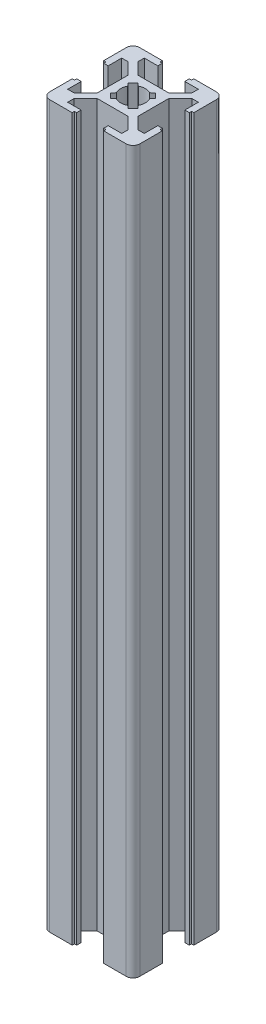
SolidWorks part; units mm, degrees
material "3.3547 (EN-AW 5083)"
ref_plane "Płaszczyzna przednia" through (0, 0, 0) normal (0, 0, 1) x (1, 0, 0)
ref_plane "Płaszczyzna górna" through (0, 0, 0) normal (0, 1, 0) x (1, 0, 0)
ref_plane "Płaszczyzna prawa" through (0, 0, 0) normal (1, 0, 0) x (0, 0, -1)
sketch "Szkic1" plane through (0, 0, 0) normal (0, 1, 0) x (1, 0, 0)
  line L0 (0, 10) -> (0, -10) construction
  line L1 (4.5, -4.5) -> (-4.5, -4.5)
  line L2 (4.5, -4.5) -> (4.5, 4.5)
  line L3 (4.5, 4.5) -> (-4.5, 4.5)
  line L4 (-4.5, -4.5) -> (-4.5, 4.5)
  line L5 (4.5, -4.5) -> (-4.5, 4.5) construction
  line L6 (4.5, 4.5) -> (-4.5, -4.5) construction
  line L7 (8.5, -10) -> (-8.5, -10)
  line L8 (10, -8.5) -> (10, 8.5)
  line L9 (8.5, 10) -> (-8.5, 10)
  line L10 (-10, -8.5) -> (-10, 8.5)
  line L11 (10, -10) -> (-10, 10) construction
  line L12 (10, 10) -> (-10, -10) construction
  line L13 (3.5, 10) -> (-3.5, 10)
  line L14 (-3.5, 10) -> (-3.5, 9.5)
  line L15 (-3.5, 9.5) -> (-3, 9.5)
  line L16 (-3, 9.5) -> (-3, 8.5)
  line L17 (-3, 8.5) -> (-6, 8.5)
  line L18 (-6, 8.5) -> (-6, 7.06)
  line L19 (-6, 7.06) -> (-3.4405, 4.5)
  line L20 (-1.9445, 3.0052) -> (-3.0052, 1.9445)
  line L21 (-1.9445, 3.0052) -> (-1.2713, 2.4385)
  line L22 (-3.0052, 1.9445) -> (-2.4385, 1.2713)
  line L23 (3.5, 10) -> (3.5, 9.5)
  line L24 (3.5, 9.5) -> (3, 9.5)
  line L25 (3, 9.5) -> (3, 8.5)
  line L26 (3, 8.5) -> (6, 8.5)
  line L27 (6, 8.5) -> (6, 7.06)
  line L28 (6, 7.06) -> (3.4405, 4.5)
  line L29 (1.9445, 3.0052) -> (3.0052, 1.9445)
  line L30 (1.9445, 3.0052) -> (1.2713, 2.4385)
  line L31 (3.0052, 1.9445) -> (2.4385, 1.2713)
  line L32 (1.9445, 3.0052) -> (1.2713, 2.4385)
  line L33 (3.0052, 1.9445) -> (1.9445, 3.0052)
  line L34 (3.0052, 1.9445) -> (2.4385, 1.2713)
  line L35 (7.06, 6) -> (4.5, 3.4405)
  line L36 (8.5, 6) -> (7.06, 6)
  line L37 (8.5, 3) -> (8.5, 6)
  line L38 (9.5, 3) -> (8.5, 3)
  line L39 (9.5, 3.5) -> (9.5, 3)
  line L40 (10, 3.5) -> (9.5, 3.5)
  line L41 (10, -3.5) -> (9.5, -3.5)
  line L42 (9.5, -3.5) -> (9.5, -3)
  line L43 (9.5, -3) -> (8.5, -3)
  line L44 (8.5, -3) -> (8.5, -6)
  line L45 (8.5, -6) -> (7.06, -6)
  line L46 (7.06, -6) -> (4.5, -3.4405)
  line L47 (3.0052, -1.9445) -> (2.4385, -1.2713)
  line L48 (3.0052, -1.9445) -> (1.9445, -3.0052)
  line L49 (1.9445, -3.0052) -> (1.2713, -2.4385)
  line L50 (3.0052, -1.9445) -> (2.4385, -1.2713)
  line L51 (1.9445, -3.0052) -> (3.0052, -1.9445)
  line L52 (1.9445, -3.0052) -> (1.2713, -2.4385)
  line L53 (6, -7.06) -> (3.4405, -4.5)
  line L54 (6, -8.5) -> (6, -7.06)
  line L55 (3, -8.5) -> (6, -8.5)
  line L56 (3, -9.5) -> (3, -8.5)
  line L57 (3.5, -9.5) -> (3, -9.5)
  line L58 (3.5, -10) -> (3.5, -9.5)
  line L59 (-3.5, -10) -> (-3.5, -9.5)
  line L60 (-3.5, -9.5) -> (-3, -9.5)
  line L61 (-3, -9.5) -> (-3, -8.5)
  line L62 (-3, -8.5) -> (-6, -8.5)
  line L63 (-6, -8.5) -> (-6, -7.06)
  line L64 (-6, -7.06) -> (-3.4405, -4.5)
  line L65 (-1.9445, -3.0052) -> (-1.2713, -2.4385)
  line L66 (-1.9445, -3.0052) -> (-3.0052, -1.9445)
  line L67 (-3.0052, -1.9445) -> (-2.4385, -1.2713)
  line L68 (-1.9445, -3.0052) -> (-1.2713, -2.4385)
  line L69 (-3.0052, -1.9445) -> (-1.9445, -3.0052)
  line L70 (-3.0052, -1.9445) -> (-2.4385, -1.2713)
  line L71 (-7.06, -6) -> (-4.5, -3.4405)
  line L72 (-8.5, -6) -> (-7.06, -6)
  line L73 (-8.5, -3) -> (-8.5, -6)
  line L74 (-9.5, -3) -> (-8.5, -3)
  line L75 (-9.5, -3.5) -> (-9.5, -3)
  line L76 (-10, -3.5) -> (-9.5, -3.5)
  line L77 (-10, 3.5) -> (-9.5, 3.5)
  line L78 (-9.5, 3.5) -> (-9.5, 3)
  line L79 (-9.5, 3) -> (-8.5, 3)
  line L80 (-8.5, 3) -> (-8.5, 6)
  line L81 (-8.5, 6) -> (-7.06, 6)
  line L82 (-7.06, 6) -> (-4.5, 3.4405)
  line L83 (-3.0052, 1.9445) -> (-2.4385, 1.2713)
  line L84 (-3.0052, 1.9445) -> (-1.9445, 3.0052)
  line L85 (-1.9445, 3.0052) -> (-1.2713, 2.4385)
  circle A0 centre (0, 0) radius 2.75
  arc A1 (10, -8.5) -> (8.5, -10) centre (8.5, -8.5) cw
  arc A2 (-10, -8.5) -> (-8.5, -10) centre (-8.5, -8.5) ccw
  arc A3 (10, 8.5) -> (8.5, 10) centre (8.5, 8.5) ccw
  arc A4 (-8.5, 10) -> (-10, 8.5) centre (-8.5, 8.5) ccw
  point P16 (0, 10)
  point P37 (-2.4749, 2.4749)
  dimension "D1" = 5.5
  dimension "D12" = 1.5
  dimension "D2" = 9
  dimension "D3" = 20
  dimension "D4" = 20
  dimension "D5" = 7
  dimension "D6" = 0.5
  dimension "D7" = 0.5
  dimension "D8" = 1
  dimension "D9" = 3
  dimension "D10" = 1.44
  dimension "D11" = 3.62
  dimension "D13" = 1.5
  dimension "D14" = 3.5
  dimension "D15" = 0.88
  dimension "D16" = 4
extrude "Dodanie-wyciągnięcie1" add sketch "Szkic1" along normal blind 160 contours L9 A4 L10 L77 L78 L79 L80 L81 L82 L4 L3 L19 L18 L17 L16 L15 L14 | L8 A3 L9 L23 L24 L25 L26 L27 L28 L3 L2 L35 L36 L37 L38 L39 L40 | L4 L1 L2 L3 A0 L47 L48 L49 L65 L66 L67 L22 L20 L21 L30 L29 L31 | L10 A2 L7 L59 L60 L61 L62 L63 L64 L1 L4 L71 L72 L73 L74 L75 L76 | A1 L8 L41 L42 L43 L44 L45 L46 L2 L1 L53 L54 L55 L56 L57 L58 L7
